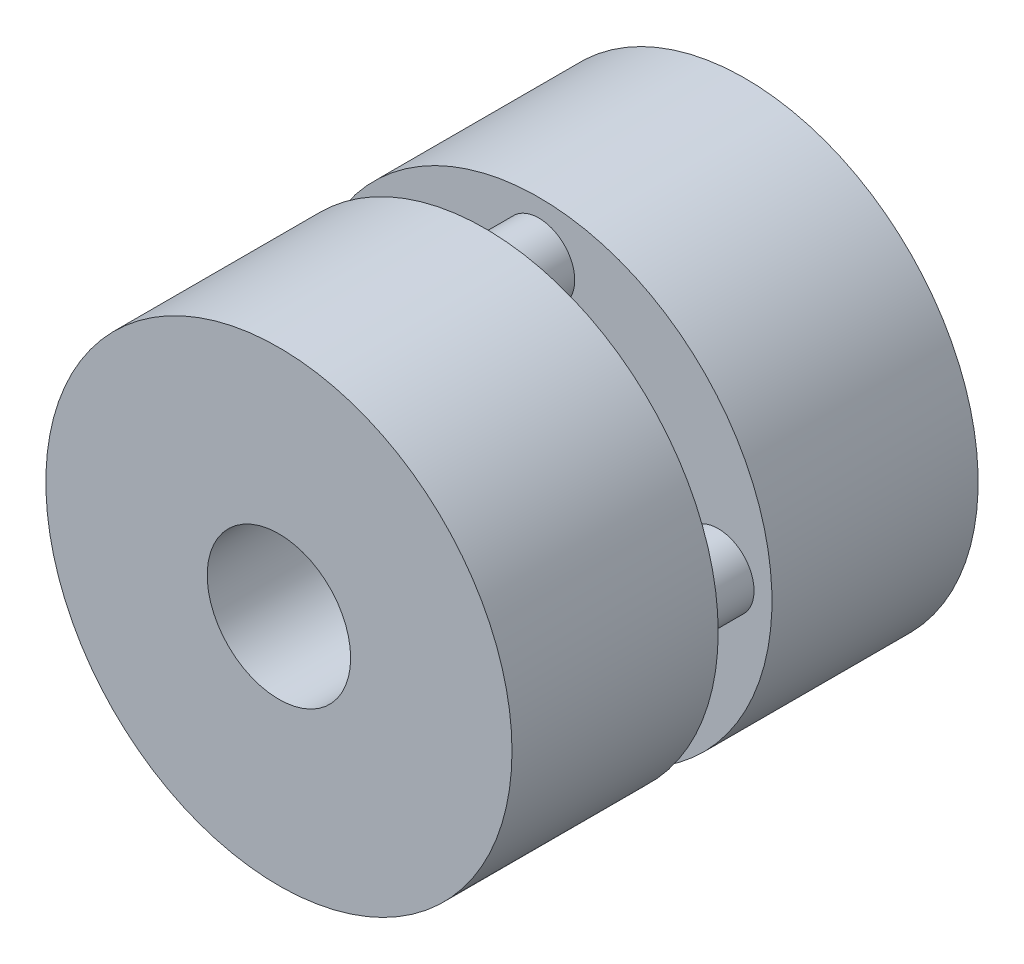
SolidWorks part; units mm, degrees
ref_plane "Front Plane" through (0, 0, 0) normal (0, 0, 1) x (1, 0, 0)
ref_plane "Top Plane" through (0, 0, 0) normal (0, 1, 0) x (1, 0, 0)
ref_plane "Right Plane" through (0, 0, 0) normal (1, 0, 0) x (0, 0, -1)
sketch "Sketch1" plane through (0, 0, 0) normal (0, 0, 1) x (1, 0, 0)
  circle A0 centre (0, 0) radius 13
  circle A1 centre (0, 0) radius 4
  dimension "D1" = 26
  dimension "D2" = 8
extrude "Boss-Extrude1" add sketch "Sketch1" along normal blind 11.5
sketch "Sketch2" plane through (0, 0, 0) normal (0, 0, -1) x (-1, 0, 0)
  circle A0 centre (0, 10) radius 2
  circle A1 centre (10, 0) radius 2
  circle A2 centre (0, -10) radius 2
  circle A3 centre (-10, 0) radius 2
  point P12 (0, 0)
  dimension "D2" = 4
  dimension "D1" = 10
  dimension "D3" = 4
extrude "Boss-Extrude2" add sketch "Sketch2" along normal blind 3
sketch "Sketch3" plane through (0, 0, -3) normal (0, 0, -1) x (-1, 0, 0)
  circle A0 centre (0, 0) radius 13
  circle A1 centre (0, 0) radius 4
  dimension "D1" = 8
  dimension "D2" = 26
extrude "Boss-Extrude3" add sketch "Sketch3" along normal blind 11.5
